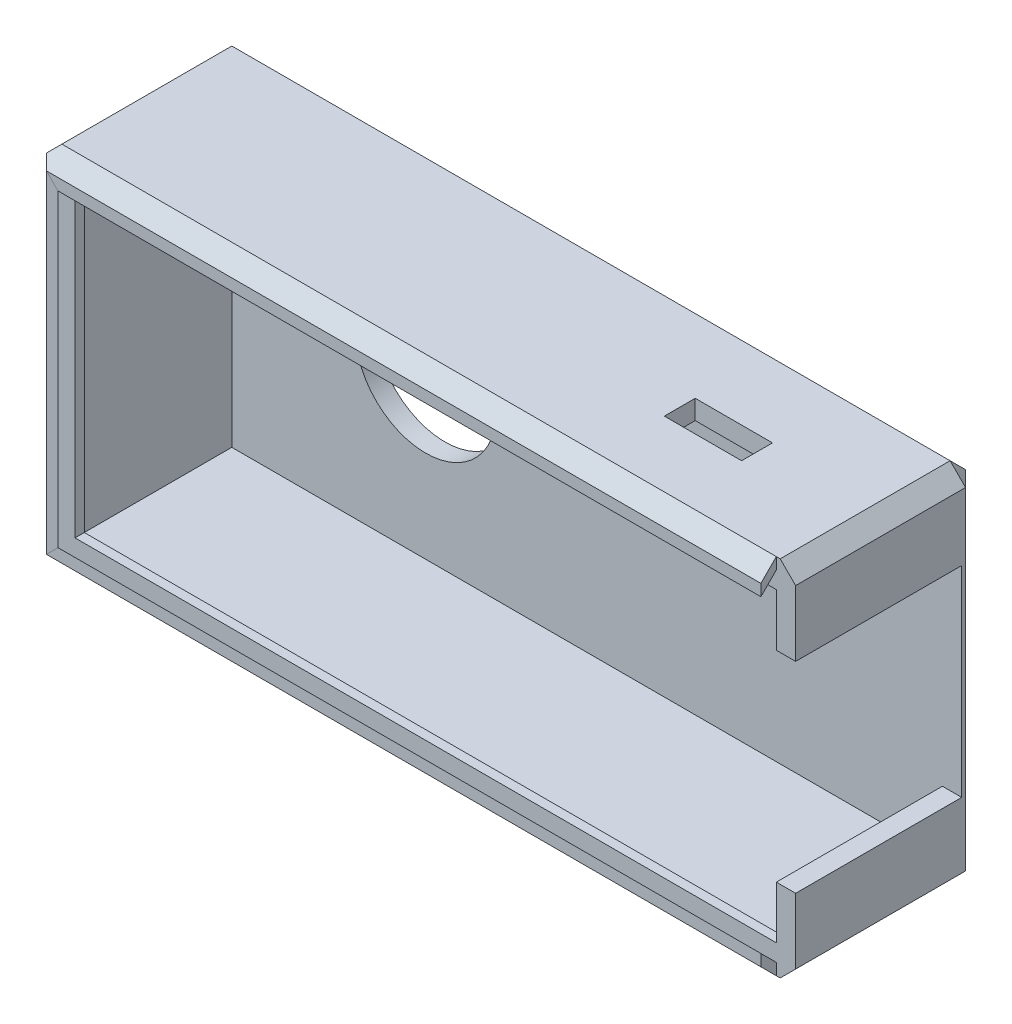
SolidWorks part; units mm, degrees
ref_plane "Front Plane" through (0, 0, 0) normal (0, 0, 1) x (1, 0, 0)
ref_plane "Top Plane" through (0, 0, 0) normal (0, 1, 0) x (1, 0, 0)
ref_plane "Right Plane" through (0, 0, 0) normal (1, 0, 0) x (0, 0, -1)
sketch "Sketch1" plane through (0, 0, 0) normal (0, 0, 1) x (1, 0, 0)
  line L1 (-24.25, 11.75) -> (24.25, 11.75)
  line L2 (-24.25, 11.75) -> (-24.25, -11.75)
  line L3 (-24.25, -11.75) -> (24.25, -11.75)
  line L4 (24.25, 11.75) -> (24.25, -11.75)
  line L5 (-24.25, 11.75) -> (24.25, -11.75) construction
  line L6 (-24.25, -11.75) -> (24.25, 11.75) construction
  point P0 (0, 0)
  dimension "D1" = 23.5
  dimension "D2" = 48.5
extrude "Boss-Extrude1" add sketch "Sketch1" along normal blind 12
shell "Shell1" thickness 1.25
sketch "Sketch2" plane through (0, 0, 1.25) normal (0, 0, 1) x (1, 0, 0)
  line L0 (-23, 10.5) -> (-23, -10.5) construction
  circle A0 centre (-10.45, 0) radius 4.55
  dimension "D1" = 9.1
  dimension "D2" = 12.55
extrude "Cut-Extrude1" cut sketch "Sketch2" against normal through all both and the other way through all
sketch "Sketch3" plane through (24.25, 0, 0) normal (1, 0, 0) x (0, 0, -1)
  line L0 (-12, -11.75) -> (-12, 11.75) construction
  line L1 (-12, -6.5) -> (-1.25, -6.5)
  line L2 (-12, -6.5) -> (-12, 6.5)
  line L3 (-12, 6.5) -> (-1.25, 6.5)
  line L4 (-1.25, -6.5) -> (-1.25, 6.5)
  line L5 (-1.25, -10.5) -> (-1.25, 10.5) construction
  dimension "D1" = 13
  dimension "D2" = 6.5
  dimension "D3" = 0
extrude "Cut-Extrude2" cut sketch "Sketch3" against normal blind 3
curve "CompCurve1"
sketch "Sketch4" plane through (23, 0, 0) normal (1, 0, 0) x (0, 0, -1)
  line L0 (-12, -11.75) -> (-13, -10.75)
  line L1 (-13, -10.75) -> (-13, -10)
  line L2 (-13, -10) -> (-12, -11)
  line L3 (-12, -11.75) -> (-12, -6.5) construction
  line L4 (-12, -11) -> (-12, -11.75)
  dimension "D1" = 0.75
  dimension "D2" = 45
  dimension "D3" = 1
sweep "Sweep2" add profiles "Sketch4" path "CompCurve1"
chamfer "Chamfer1" distance 1 angle 45 8 edges at (24.25, 0, 0) (0, 11.75, 0) (-24.25, 11.75, 6) (-24.25, 0, 0) (24.25, -11.75, 6) (-24.25, -11.75, 6) (0, -11.75, 0) (24.25, 11.75, 6)
sketch "Sketch5" plane through (0, 11.75, 0) normal (0, 1, 0) x (1, 0, 0)
  line L2 (23, -12) -> (23, -1.25) construction
  line L3 (16.5, -7.75) -> (11.5, -7.75)
  line L4 (16.5, -7.75) -> (16.5, -5.75)
  line L5 (16.5, -5.75) -> (11.5, -5.75)
  line L6 (11.5, -7.75) -> (11.5, -5.75)
  line L7 (16.5, -7.75) -> (11.5, -5.75) construction
  line L8 (16.5, -5.75) -> (11.5, -7.75) construction
  line L9 (23, -1.25) -> (-23, -1.25) construction
  point P2 (14, -6.75)
  dimension "D1" = 9
  dimension "D2" = 5.5
  dimension "D3" = 2
  dimension "D4" = 5
extrude "Cut-Extrude3" cut sketch "Sketch5" against normal up to next
sketch "Sketch6" plane through (23, 0, 0) normal (-1, 0, 0) x (0, 0, 1)
  line L1 (12, -10.5) -> (11.4, -10.5)
  line L2 (12, -10.5) -> (12, -9.9)
  line L3 (12, -9.9) -> (11.4, -9.9)
  line L4 (11.4, -10.5) -> (11.4, -9.9)
  dimension "D1" = 0.6
  dimension "D2" = 0.6
sweep "Sweep3" add profiles "Sketch6" path "CompCurve1"
